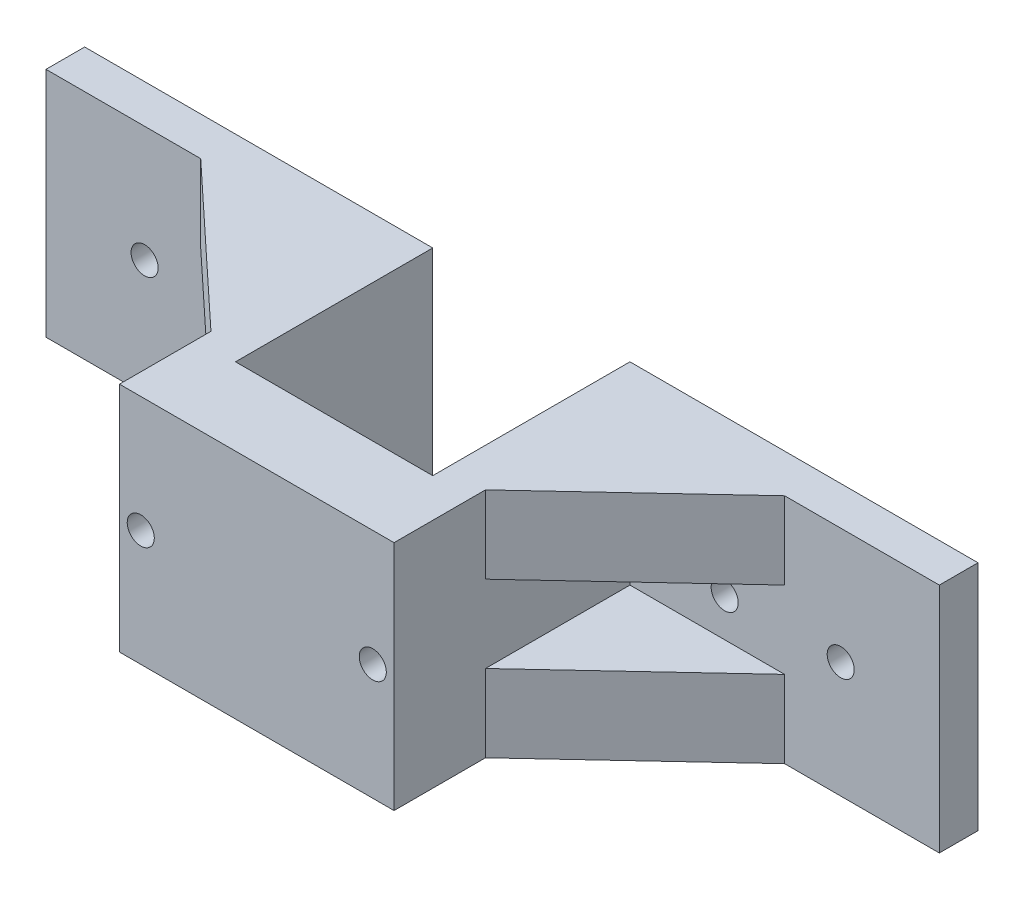
SolidWorks part; units mm, degrees
ref_plane "前视基准面" through (0, 0, 0) normal (0, 0, 1) x (1, 0, 0)
ref_plane "上视基准面" through (0, 0, 0) normal (0, 1, 0) x (1, 0, 0)
ref_plane "右视基准面" through (0, 0, 0) normal (1, 0, 0) x (0, 0, -1)
sketch "草图1" plane through (0, 0, 0) normal (0, 0, 1) x (1, 0, 0)
  line L1 (20, -15) -> (-20, -15)
  line L2 (20, -15) -> (20, 15)
  line L3 (20, 15) -> (-20, 15)
  line L4 (-20, -15) -> (-20, 15)
  line L5 (0, 15) -> (0, -15) construction
  line L6 (20, 0) -> (-20, 0) construction
  point P0 (0, 0)
  dimension "D1" = 30
  dimension "D2" = 40
extrude "凸台-拉伸1" add sketch "草图1" along normal blind 5
sketch "草图2" plane through (20, 0, 0) normal (1, 0, 0) x (0, 0, -1)
  line L0 (0, 15) -> (-25.5, 15)
  line L1 (-25.5, 15) -> (-25.5, -15)
  line L2 (-25.5, -15) -> (0, -15)
  line L3 (0, -15) -> (0, 15)
  dimension "D1" = 25.5
extrude "凸台-拉伸2" add sketch "草图2" along normal blind 5
sketch "草图3" plane through (20, 0, 0) normal (-1, 0, 0) x (0, 0, 1)
  line L1 (30.5, -15) -> (25.5, -15)
  line L2 (30.5, -15) -> (30.5, 15)
  line L3 (30.5, 15) -> (25.5, 15)
  line L4 (25.5, -15) -> (25.5, 15)
  line L5 (28, 15) -> (28, -15) construction
  line L6 (30.5, 0) -> (25.5, 0) construction
  point P0 (28, 0)
  dimension "D1" = 5
extrude "凸台-拉伸3" add sketch "草图3" against normal blind 30.5
sketch "草图5" plane through (50.5, 0, 0) normal (1, 0, 0) x (0, 0, -1)
  line L0 (-30.5, 15) -> (0, 15)
  line L1 (0, 15) -> (0, -15)
  line L2 (0, -15) -> (-30.5, -15)
  line L3 (-30.5, -15) -> (-30.5, 15)
extrude "凸台-拉伸4" add sketch "草图5" along normal blind 5
sketch "草图6" plane through (55.5, 0, 0) normal (1, 0, 0) x (0, 0, -1)
  line L0 (0, 15) -> (-5, 15)
  line L1 (0, 15) -> (-30.5, 15) construction
  line L2 (-5, 15) -> (-5, -15)
  line L3 (-30.5, -15) -> (0, -15) construction
  line L4 (-5, -15) -> (0, -15)
  line L5 (0, -15) -> (0, 15)
  dimension "D1" = 5
extrude "凸台-拉伸5" add sketch "草图6" along normal blind 40
sketch "草图9" plane through (0, -15, 0) normal (0, -1, 0) x (1, 0, 0)
  line L0 (55.5, 23.6748) -> (75.5, 5)
  line L1 (55.5, 26.5) -> (55.5, 5) construction
  line L2 (95.5, 5) -> (55.5, 5) construction
rib "筋1" sketch "草图9" sketch "草图9" thickness 10 extrusion direction parallel to sketch draft on no parameters "D1"=10
ref_plane "基准面1" through (0, 0, 0) normal (0, 1, 0) x (1, 0, 0)
mirror "镜向1" about plane through (0, 0, 0) normal (0, 1, 0) of "筋1"
ref_plane "基准面2" through (37.75, 0, 0) normal (1, 0, 0) x (0, 0, -1)
mirror "镜向2" about plane through (37.75, 0, 0) normal (1, 0, 0) of "镜向1", "筋1"
sketch "草图10" plane through (0, 0, 0) normal (0, 0, -1) x (-1, 0, 0)
  line L0 (-37.75, 15) -> (-37.75, -42.7043) construction
  line L1 (-50.5, 15) -> (-25, 15) construction
  circle A0 centre (-52.75, 0) radius 1.75
  circle A1 centre (-22.75, 0) radius 1.75
  circle A2 centre (-82.75, 0) radius 1.75
  circle A3 centre (7.25, 0) radius 1.75
  dimension "D1" = 3.5
  dimension "D3" = 3.5
  dimension "D2" = 30
  dimension "D4" = 30
extrude "切除-拉伸1" cut sketch "草图10" against normal blind 82
sketch "草图11" plane through (0, 0, 0) normal (0, 0, -1) x (-1, 0, 0)
  line L0 (-37.75, 15) -> (-37.75, -15) construction
  line L1 (-50.5, 15) -> (-25, 15) construction
  line L2 (-50.5, -15) -> (-25, -15) construction
  circle A0 centre (-67.75, 0) radius 1.75
  circle A1 centre (-82.75, 0) radius 1.75 construction
  circle A2 centre (-7.75, 0) radius 1.75
  dimension "D1" = 3.5
  dimension "D2" = 15
extrude "切除-拉伸2" cut sketch "草图11" against normal blind 40
sketch "草图12" plane through (0, 0, 30.5) normal (0, 0, 1) x (1, 0, 0)
  line L0 (20, 15) -> (20, -15)
  line L1 (20, -15) -> (55.5, -15)
  line L2 (55.5, -15) -> (55.5, 15)
  line L3 (55.5, 15) -> (20, 15)
extrude "凸台-拉伸6" add sketch "草图12" along normal blind 5
sketch "草图13" plane through (0, 0, 0) normal (0, 0, -1) x (-1, 0, 0)
  circle A0 centre (-52.75, 0) radius 1.75 construction
  circle A1 centre (-22.75, 0) radius 1.75 construction
  circle A2 centre (-22.75, 0) radius 1.75
  circle A3 centre (-52.75, 0) radius 1.75
extrude "切除-拉伸3" cut sketch "草图13" against normal blind 66
